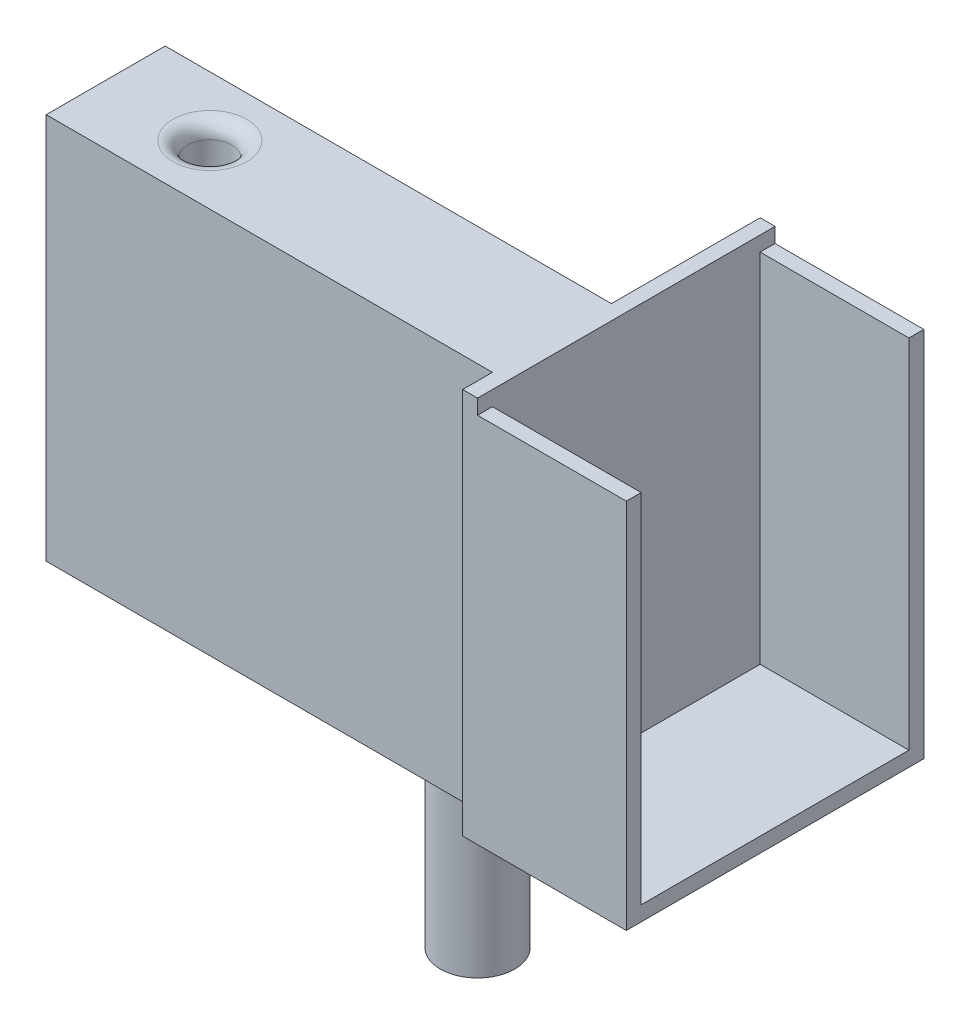
SolidWorks part; units mm, degrees
ref_plane "Front Plane" through (0, 0, 0) normal (0, 0, 1) x (1, 0, 0)
ref_plane "Top Plane" through (0, 0, 0) normal (0, 1, 0) x (1, 0, 0)
ref_plane "Right Plane" through (0, 0, 0) normal (1, 0, 0) x (0, 0, -1)
sketch "Sketch1" plane through (0, 0, 0) normal (0, 0, 1) x (1, 0, 0)
  line L1 (0, 0) -> (76.2, 0)
  line L2 (0, 0) -> (0, 66.04)
  line L3 (0, 66.04) -> (76.2, 66.04)
  line L4 (76.2, 0) -> (76.2, 66.04)
  dimension "D1" = 66.04
  dimension "D2" = 76.2
extrude "Boss-Extrude1" add sketch "Sketch1" along normal blind 20.32
sketch "Sketch2" plane through (0, 66.04, 0) normal (0, 1, 0) x (1, 0, 0)
  line L0 (0, -20.32) -> (0, 0) construction
  line L2 (76.2, -20.32) -> (76.2, 0) construction
  circle A0 centre (17.78, -10.16) radius 3.75
  point P2 (0, -10.16)
  point P5 (76.2, -10.16)
  dimension "D3" = 7.5
  dimension "D1" = 17.78
  dimension "D2" = 0
extrude "Cut-Extrude1" cut sketch "Sketch2" against normal blind 57.15
sketch "Sketch3" plane through (76.2, 0, 0) normal (1, 0, 0) x (0, 0, -1)
  line L0 (-20.32, 0) -> (-20.32, 66.04) construction
  line L1 (-3.16, 5.08) -> (-17.16, 5.08)
  line L2 (-3.16, 5.08) -> (-3.16, 12.08)
  line L3 (-3.16, 12.08) -> (-17.16, 12.08)
  line L4 (-17.16, 5.08) -> (-17.16, 12.08)
  line L5 (-3.16, 5.08) -> (-17.16, 12.08) construction
  line L6 (-3.16, 12.08) -> (-17.16, 5.08) construction
  line L9 (0, 0) -> (0, 66.04) construction
  line L10 (-20.32, 66.04) -> (0, 66.04) construction
  point P0 (-10.16, 8.58)
  point P9 (-10.16, 8.58)
  dimension "D1" = 60.96
  dimension "D2" = 14
  dimension "D3" = 7
  dimension "D4" = 14
  dimension "D5" = 10.16
  dimension "D6" = 3.16
sketch "Sketch4" plane through (0, 0, 0) normal (0, -1, 0) x (-1, 0, 0)
  line L1 (-6.16, -14.16) -> (-14.16, -14.16)
  line L2 (-6.16, -14.16) -> (-6.16, -6.16)
  line L3 (-6.16, -6.16) -> (-14.16, -6.16)
  line L4 (-14.16, -14.16) -> (-14.16, -6.16)
  line L5 (-6.16, -14.16) -> (-14.16, -6.16) construction
  line L6 (-6.16, -6.16) -> (-14.16, -14.16) construction
  line L7 (0, -20.32) -> (-76.2, -20.32) construction
  line L8 (0, -20.32) -> (0, 0) construction
  point P0 (-10.16, -10.16)
  point P10 (0, -10.16)
  dimension "D1" = 8
  dimension "D2" = 8
  dimension "D3" = 10.16
  dimension "D4" = 10.16
extrude "Cut-Extrude4" cut sketch "Sketch4" against normal blind 5.08 contours L1 L4 L3 L2
fillet "Fillet2" radius 2.54 1 edges at (17.78, 66.04, 13.91)
sketch "Sketch5" plane through (76.2, 0, 0) normal (1, 0, 0) x (0, 0, -1)
  line L0 (-20.32, 0) -> (-20.32, 66.04) construction
  line L1 (-25.4, 66.04) -> (25.4, 66.04)
  line L2 (-25.4, 66.04) -> (-25.4, 0)
  line L3 (-25.4, 0) -> (25.4, 0)
  line L4 (25.4, 66.04) -> (25.4, 0)
  dimension "D1" = 50.8
  dimension "D2" = 5.08
extrude "Boss-Extrude2" add sketch "Sketch5" along normal blind 2.54
sketch "Sketch6" plane through (78.74, 0, 0) normal (1, 0, 0) x (0, 0, -1)
  line L0 (25.4, 66.04) -> (-25.4, 66.04) construction
  line L1 (-25.4, 0) -> (-19.6314, 0)
  line L2 (-25.4, 0) -> (-25.4, 63.5)
  line L3 (-25.4, 63.5) -> (-22.86, 63.5)
  line L4 (-22.86, 2.54) -> (-22.86, 63.5)
  line L5 (25.4, 0) -> (15.24, 0)
  line L6 (25.4, 0) -> (25.4, 63.5)
  line L7 (25.4, 63.5) -> (22.86, 63.5)
  line L8 (22.86, 2.54) -> (22.86, 63.5)
  line L9 (-19.6314, 0) -> (15.24, 0)
  line L11 (-22.86, 2.54) -> (22.86, 2.54)
  line L13 (-25.4, 66.04) -> (-25.4, 0) construction
  dimension "D1" = 2.54
  dimension "D2" = 2.54
  dimension "D3" = 2.54
  dimension "D4" = 2.54
  dimension "D5" = 2.54
  dimension "D6" = 0
extrude "Boss-Extrude3" add sketch "Sketch6" along normal blind 25.4
extrude "Cut-Extrude5" cut sketch "Sketch3" against normal blind 73.66 and the other way up to next contours L3 L4 L1 L2
sketch "Sketch7" plane through (0, 0, 0) normal (0, -1, 0) x (-1, 0, 0)
  line L1 (0, 0) -> (-76.2, 0) construction
  line L2 (-104.14, -25.4) -> (-104.14, 25.4) construction
  circle A0 centre (-63.5, -10.16) radius 6.35
  dimension "D1" = 10.16
  dimension "D2" = 40.64
extrude "Boss-Extrude4" add sketch "Sketch7" along normal blind 30.48
